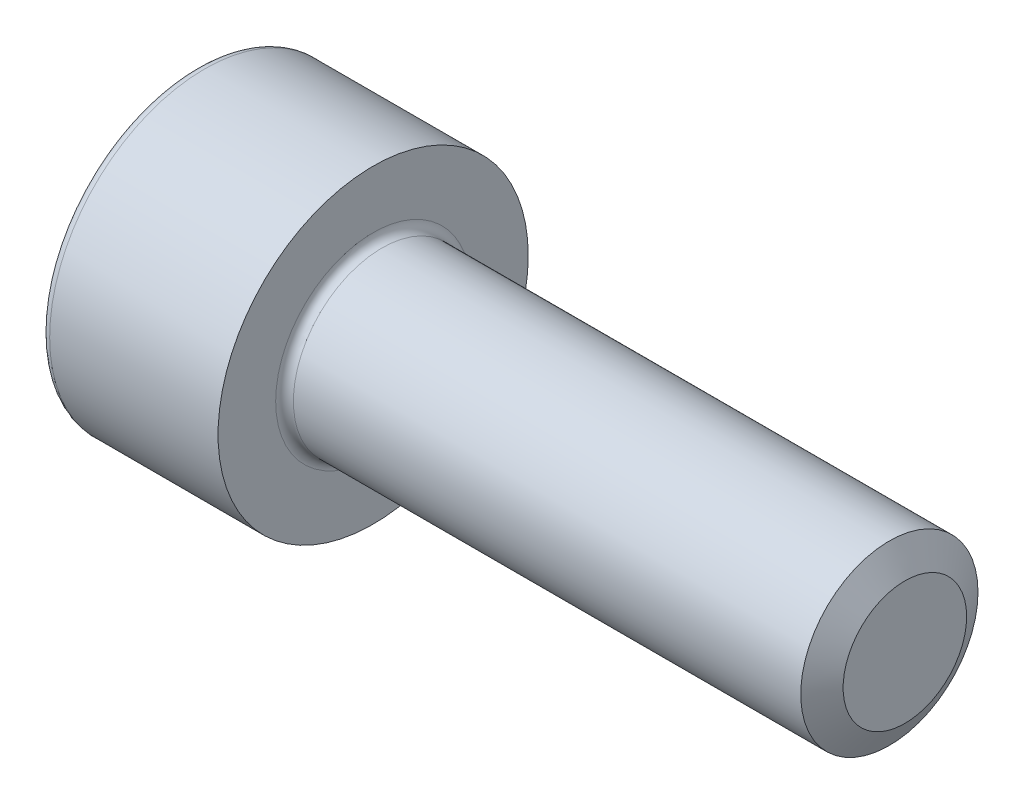
SolidWorks part; units mm, degrees
material "AISI 304"
ref_plane "前视基准面" through (0, 0, 0) normal (0, 0, 1) x (1, 0, 0)
ref_plane "上视基准面" through (0, 0, 0) normal (0, 1, 0) x (1, 0, 0)
ref_plane "右视基准面" through (0, 0, 0) normal (1, 0, 0) x (0, 0, -1)
sketch "草图1" plane through (0, 0, 0) normal (0, 0, 1) x (1, 0, 0)
  line L0 (0, 3.5) -> (0, 0)
  line L1 (0, 0) -> (4, 0)
  line L2 (4, 0) -> (4, 3.5)
  line L3 (4, 3.5) -> (0, 3.5)
  line L4 (0, 0) -> (4, 0) construction
revolve "旋转1" add sketch "草图1" angle 360 about L4
sketch "草图2" plane through (4, 0, 0) normal (1, 0, 0) x (0, 0, -1)
  circle A0 centre (0, 0) radius 2
extrude "凸台-拉伸1" add sketch "草图2" along normal blind 12
sketch "草图3" plane through (0, 0, 0) normal (-1, 0, 0) x (0, 0, 1)
  line L0 (0, 1.72) -> (-1.4896, 0.86)
  line L1 (-1.4896, 0.86) -> (-1.4896, -0.86)
  line L2 (-1.4896, -0.86) -> (0, -1.72)
  line L3 (0, -1.72) -> (1.4896, -0.86)
  line L4 (1.4896, -0.86) -> (1.4896, 0.86)
  line L5 (1.4896, 0.86) -> (0, 1.72)
extrude "切除-拉伸1" cut sketch "草图3" against normal blind 2
chamfer "倒角1" distance 0.6062 angle 30.001 1 edges at (16, 0, -2)
fillet "圆角1" radius 0.2 2 edges at (4, 0, -2) (0, 0, -3.5)
